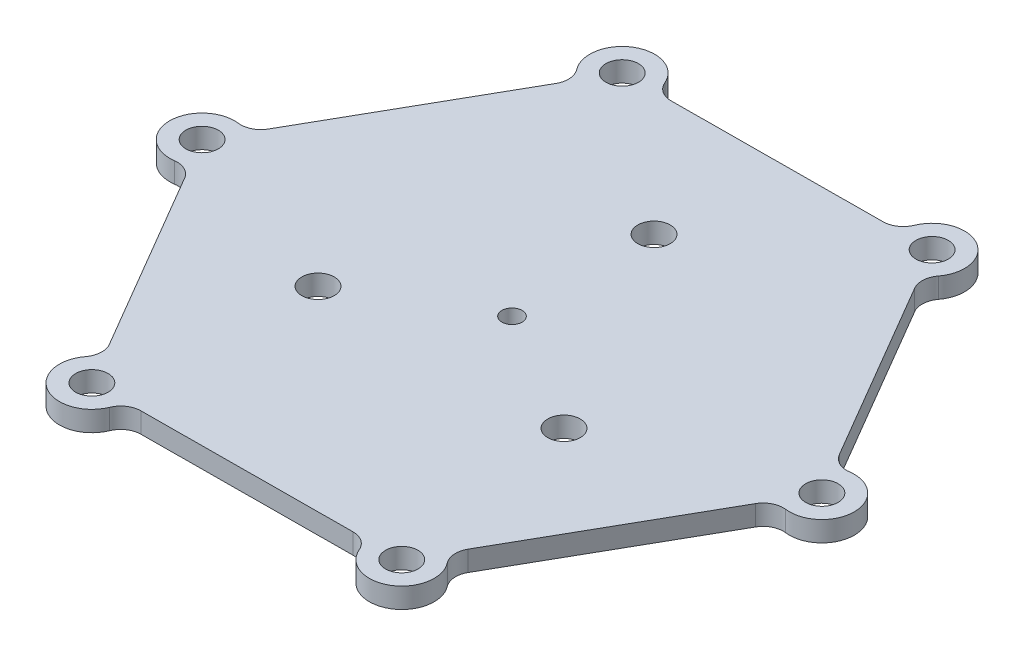
SolidWorks part; units mm, degrees
ref_plane "Plan de face" through (0, 0, 0) normal (0, 0, 1) x (1, 0, 0)
ref_plane "Plan de dessus" through (0, 0, 0) normal (0, 1, 0) x (1, 0, 0)
ref_plane "Plan de droite" through (0, 0, 0) normal (1, 0, 0) x (0, 0, -1)
sketch "Esquisse1" plane through (0, 0, 0) normal (0, 1, 0) x (1, 0, 0)
  line L0 (0, 0) -> (0, 145.9198) construction
  line L1 (88.5892, -110.1819) -> (139.9662, -19.9389)
  line L2 (139.7149, 21.6295) -> (87.2507, 111.2448)
  line L3 (51.1257, 131.8115) -> (-52.7155, 131.1837)
  line L4 (-88.5892, 110.1819) -> (-139.9662, 19.9389)
  line L5 (-139.7149, -21.6295) -> (-87.2507, -111.2448)
  line L6 (-51.1257, -131.8115) -> (52.7155, -131.1837)
  circle A0 centre (0, 0) radius 131.5 construction
  arc A1 (-149.8811, 14.9617) -> (-149.6892, -16.7726) centre (-151.8403, -0.9179) ccw
  circle A2 centre (0, 0) radius 70 construction
  arc A3 (-61.9833, 137.2817) -> (-89.3701, 121.2484) centre (-76.7151, 131.0387) ccw
  arc A4 (87.8978, 122.32) -> (60.3191, 138.021) centre (75.1253, 131.9565) ccw
  arc A5 (149.8811, -14.9617) -> (149.6892, 16.7726) centre (151.8403, 0.9179) ccw
  arc A6 (61.9833, -137.2817) -> (89.3701, -121.2484) centre (76.7151, -131.0387) ccw
  arc A7 (-87.8978, -122.32) -> (-60.3191, -138.021) centre (-75.1253, -131.9565) ccw
  arc A8 (-139.9662, 19.9389) -> (-149.8811, 14.9617) centre (-148.6565, 24.8865) cw
  arc A9 (-139.7149, -21.6295) -> (-149.6892, -16.7726) centre (-148.3448, -26.6818) ccw
  arc A10 (-87.8978, -122.32) -> (-87.2507, -111.2448) centre (-95.8806, -116.2971) ccw
  arc A11 (-60.3191, -138.021) -> (-51.1257, -131.8115) centre (-51.0653, -141.8113) cw
  arc A12 (61.9833, -137.2817) -> (52.7155, -131.1837) centre (52.7759, -141.1836) ccw
  arc A13 (89.3701, -121.2484) -> (88.5892, -110.1819) centre (97.2795, -115.1295) cw
  arc A14 (149.8811, -14.9617) -> (139.9662, -19.9389) centre (148.6565, -24.8865) ccw
  arc A15 (149.6892, 16.7726) -> (139.7149, 21.6295) centre (148.3448, 26.6818) cw
  arc A16 (87.8978, 122.32) -> (87.2507, 111.2448) centre (95.8806, 116.2971) ccw
  arc A17 (60.3191, 138.021) -> (51.1257, 131.8115) centre (51.0653, 141.8113) cw
  arc A18 (-61.9833, 137.2817) -> (-52.7155, 131.1837) centre (-52.7759, 141.1836) ccw
  arc A19 (-89.3701, 121.2484) -> (-88.5892, 110.1819) centre (-97.2795, 115.1295) cw
  circle A20 centre (-151.8403, -0.9179) radius 8
  circle A21 centre (-76.7151, 131.0387) radius 8
  circle A22 centre (75.1253, 131.9565) radius 8
  circle A23 centre (151.8403, 0.9179) radius 8
  circle A24 centre (76.7151, -131.0387) radius 8
  circle A25 centre (-75.1253, -131.9565) radius 8
  circle A26 centre (0, 70) radius 8
  circle A27 centre (60.6218, -35) radius 8
  circle A28 centre (-60.6218, -35) radius 8
  circle A29 centre (0, 0) radius 5
  point P25 (0, 0)
  point P62 (0, 0)
  point P69 (0, 0)
  point P70 (0, 0)
  dimension "D1" = 6
  dimension "D3" = 10
  dimension "D4" = 6
  dimension "D5" = 3
  dimension "D2" = 263
extrude "Boss.-Extru.2" add sketch "Esquisse1" against normal blind 10
sketch "Esquisse3" plane through (0, -10, 0) normal (0, -1, 0) x (1, 0, 0)
  circle A0 centre (0, 0) radius 110
